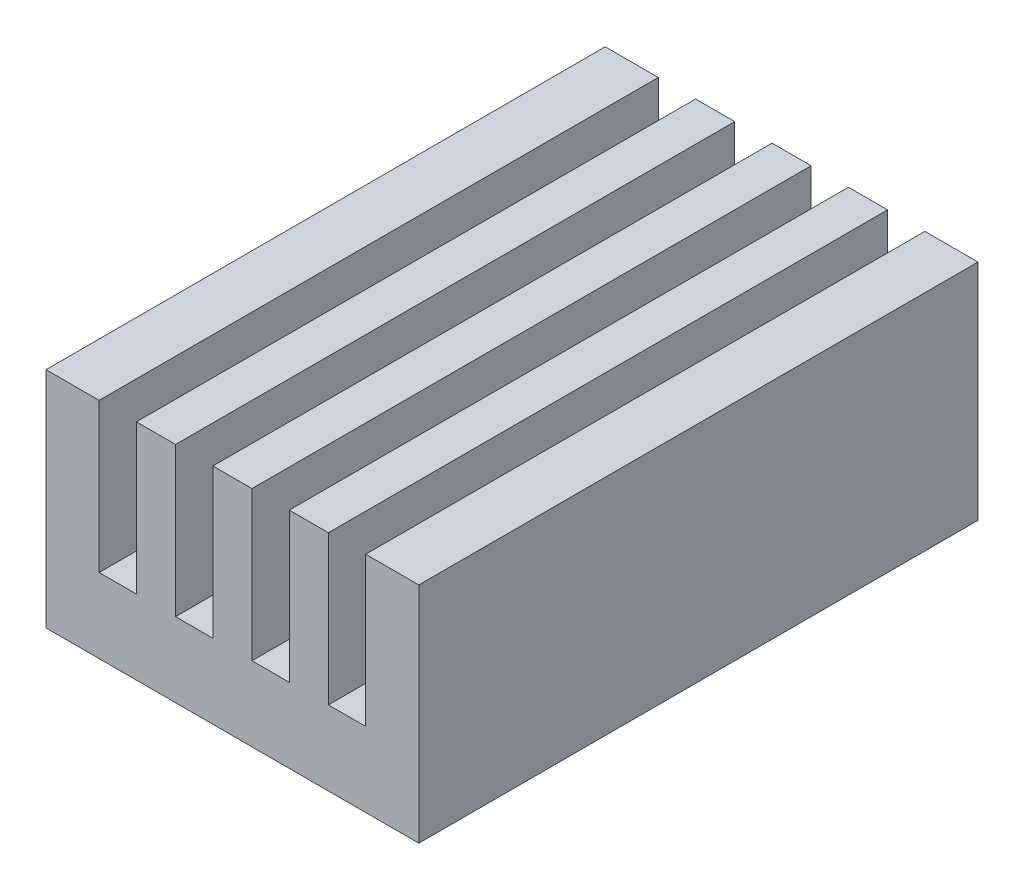
SolidWorks part; units mm, degrees
material "6061-T6 (SS)"
ref_plane "Front Plane" through (0, 0, 0) normal (0, 0, 1) x (1, 0, 0)
ref_plane "Top Plane" through (0, 0, 0) normal (0, 1, 0) x (1, 0, 0)
ref_plane "Right Plane" through (0, 0, 0) normal (1, 0, 0) x (0, 0, -1)
sketch "Sketch1" plane through (0, 0, 0) normal (0, 0, 1) x (1, 0, 0)
  line L0 (-5, 6) -> (-5, 0)
  line L1 (-5, 6) -> (5, 6)
  line L2 (-5, 0) -> (5, 0)
  line L3 (5, 6) -> (5, 0)
  line L4 (-5, 6) -> (5, 0) construction
  line L5 (-5, 0) -> (5, 6) construction
  line L8 (0, 6) -> (0, 0) construction
  line L9 (-0.525, 6) -> (-0.525, 2)
  line L10 (0.525, 6) -> (1.525, 6)
  line L11 (0.525, 6) -> (0.525, 2)
  line L12 (0.525, 2) -> (1.525, 2)
  line L13 (1.525, 6) -> (1.525, 2)
  line L14 (2.575, 6) -> (3.575, 6)
  line L15 (2.575, 6) -> (2.575, 2)
  line L16 (2.575, 2) -> (3.575, 2)
  line L17 (3.575, 6) -> (3.575, 2)
  line L18 (-0.525, 2) -> (-1.525, 2)
  line L19 (-1.525, 6) -> (-1.525, 2)
  line L20 (-2.575, 6) -> (-2.575, 2)
  line L21 (-2.575, 2) -> (-3.575, 2)
  line L22 (-3.575, 6) -> (-3.575, 2)
  point P1 (0, 3)
  point P3 (0, 0)
  dimension "D1" = 10
  dimension "D2" = 6
  dimension "D6" = 1
  dimension "D7" = 0.525
  dimension "D8" = 4
  dimension "D9" = 1.05
  dimension "D10" = 1
extrude "Boss-Extrude1" add sketch "Sketch1" along normal blind 15
equation "\"D10@Sketch1\"=\"D6@Sketch1\""
